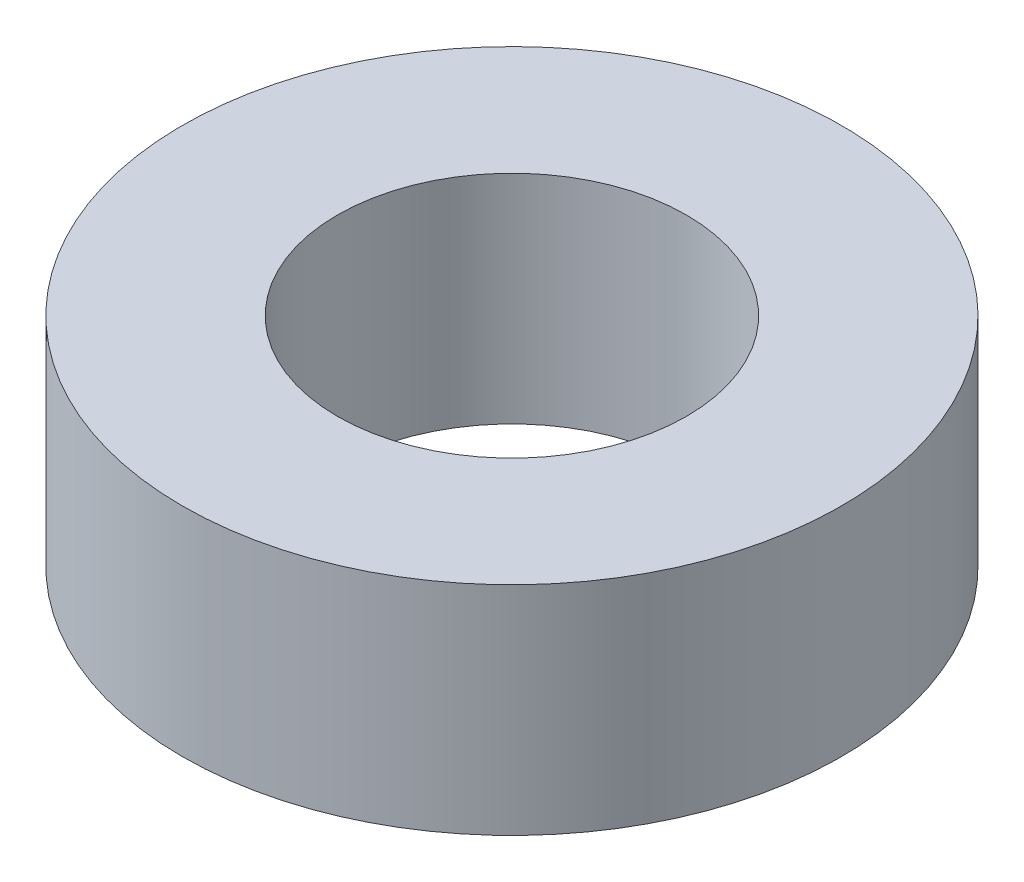
SolidWorks part; units mm, degrees
ref_plane "Front Plane" through (0, 0, 0) normal (0, 0, 1) x (1, 0, 0)
ref_plane "Top Plane" through (0, 0, 0) normal (0, 1, 0) x (1, 0, 0)
ref_plane "Right Plane" through (0, 0, 0) normal (1, 0, 0) x (0, 0, -1)
sketch "Sketch1" plane through (0, 0, 0) normal (0, 1, 0) x (1, 0, 0)
  circle A0 centre (0, 0) radius 5.715
  circle A1 centre (0, 0) radius 10.795
  point P4 (0, 10.795)
  point P5 (0, 5.715)
  dimension "D1" = 11.43
  dimension "D2" = 5.08
extrude "Boss-Extrude1" add sketch "Sketch1" along normal blind 7.112
